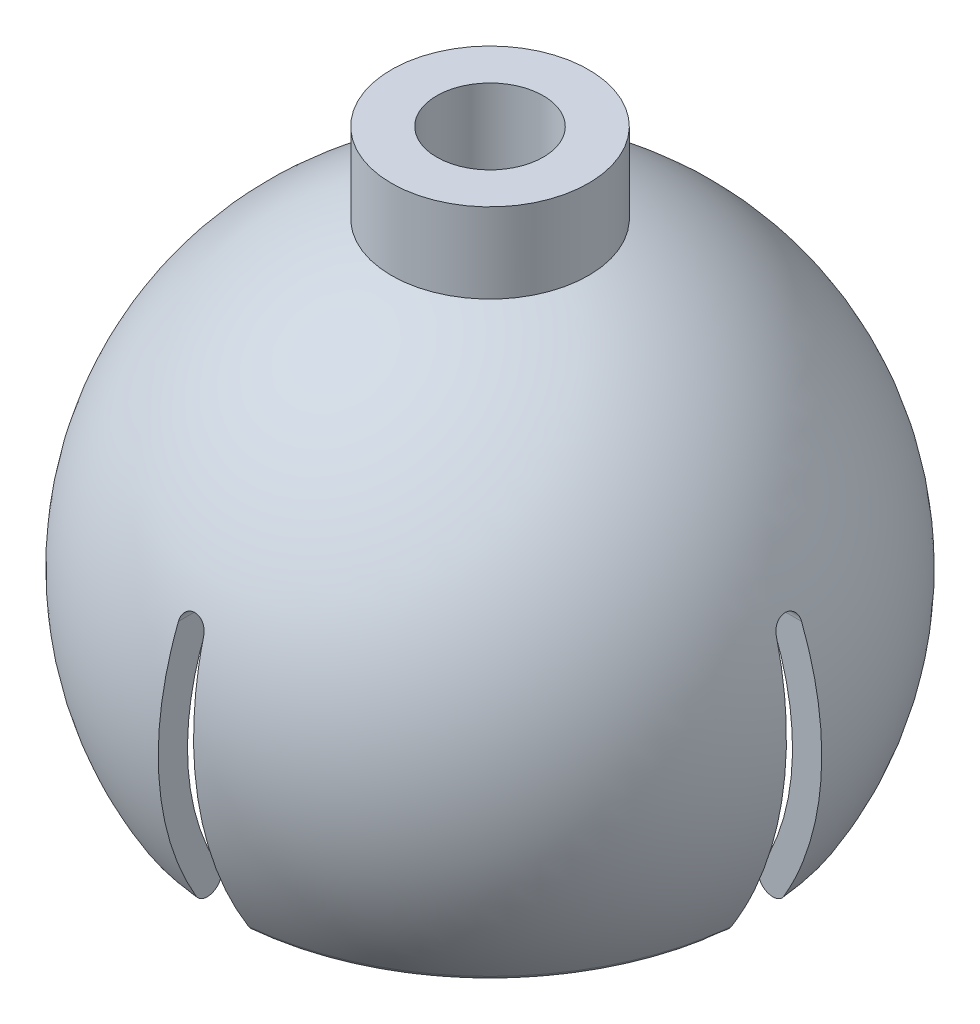
SolidWorks part; units mm, degrees
ref_plane "Front Plane" through (0, 0, 0) normal (0, 0, 1) x (1, 0, 0)
ref_plane "Top Plane" through (0, 0, 0) normal (0, 1, 0) x (1, 0, 0)
ref_plane "Right Plane" through (0, 0, 0) normal (1, 0, 0) x (0, 0, -1)
sketch "Sketch1" plane through (0, 0, 0) normal (0, 1, 0) x (1, 0, 0)
  circle A0 centre (0, 0) radius 3.7
  circle A1 centre (0, 0) radius 2
  dimension "D1" = 7.4
  dimension "D2" = 4
extrude "Boss-Extrude1" add sketch "Sketch1" along normal blind 3
sketch "Sketch2" plane through (0, 0, 0) normal (1, 0, 0) x (0, 0, -1)
  line L0 (-3.7, 0) -> (3.7, 0) construction
  line L1 (0, 0) -> (3.7, 0)
  line L2 (0, 0) -> (0, -13) construction
  line L3 (-1.5, 0) -> (-1.5, -2.8) construction
  line L4 (0, -2.8) -> (1.5, -2.8)
  line L5 (1.5, -2.8) -> (1.5, -1.6)
  line L6 (-21.9718, -13) -> (24.2421, -13) construction
  line L7 (10.1, -17.5) -> (9.2414, -16.9873) construction
  line L8 (10.1, -17.5) -> (9.2145, -18.9829) construction
  line L9 (0, 0) -> (0, -2.8)
  line L10 (-3.7, 0) -> (-1.5, 0) construction
  line L11 (-1.5, 0) -> (0, 0) construction
  line L12 (-1.5, -2.8) -> (0, -2.8) construction
  circle A0 centre (0, -13) radius 10 construction
  arc A1 (3.7, 0) -> (10.1, -17.5) centre (-0.2028, -11.3476) cw
  arc A3 (1.5, -1.6) -> (9.2414, -16.9873) centre (0.479, -11.7547) cw
  arc A4 (9.2414, -16.9873) -> (10.1, -17.5) centre (9.6707, -17.2437) ccw
  dimension "D1" = 20
  dimension "D5" = 4.5
  dimension "D8" = 12
  dimension "D9" = 1
  dimension "D2" = 13
  dimension "D3" = 3
  dimension "D4" = 2.8
  dimension "D6" = 6.4
  dimension "D7" = 1.6
revolve "Revolve1" add sketch "Sketch2" angle 360 about L2
sketch "Sketch3" plane through (0, 0, 0) normal (1, 0, 0) x (0, 0, -1)
  line L0 (-9.6707, -17.7437) -> (9.6707, -17.7437) construction
  line L1 (-1, -17.7437) -> (1, -17.7437)
  line L2 (-1, -17.7437) -> (-0.4746, -7.7188)
  line L3 (0, 0) -> (0, -21.3773) construction
  line L4 (1, -17.7437) -> (0.4746, -7.7188)
  line L5 (-9.6707, -17.7437) -> (-1, -17.7437) construction
  line L6 (1, -17.7437) -> (9.6707, -17.7437) construction
  arc A0 (-0.4746, -7.7188) -> (0.4746, -7.7188) centre (0, -7.7437) cw
  dimension "D2" = 10
  dimension "D1" = 2
  dimension "D3" = 87
extrude "Cut-Extrude1" cut sketch "Sketch3" against normal through all both and the other way through all contours L2 A0 L4 L1
pattern_circular "CirPattern1" count 4 over 360 about axis through (0, 0, 0) along (0, 1, 0) of "Cut-Extrude1"
